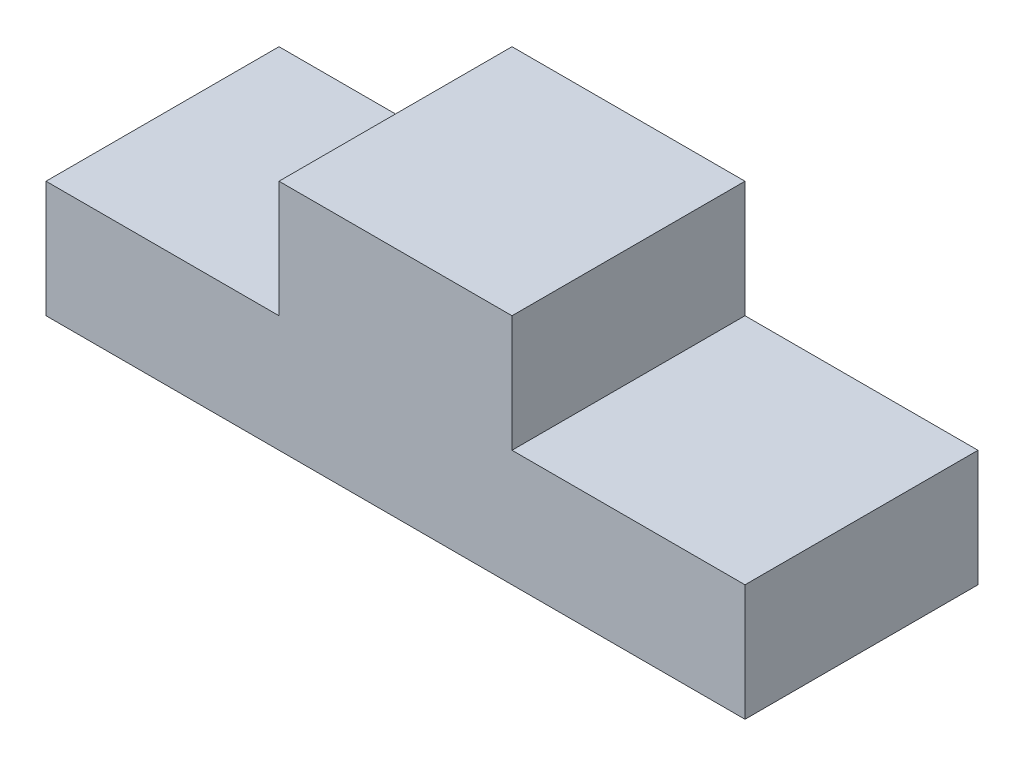
SolidWorks part; units mm, degrees
ref_plane "Front Plane" through (0, 0, 0) normal (0, 0, 1) x (1, 0, 0)
ref_plane "Top Plane" through (0, 0, 0) normal (0, 1, 0) x (1, 0, 0)
ref_plane "Right Plane" through (0, 0, 0) normal (1, 0, 0) x (0, 0, -1)
sketch "Sketch1" plane through (0, 0, 0) normal (0, 0, 1) x (1, 0, 0)
  line L0 (0, 12.7) -> (25.4, 12.7)
  line L1 (0, 0) -> (76.2, 0)
  line L2 (0, 0) -> (0, 12.7)
  line L3 (25.4, 25.4) -> (50.8, 25.4)
  line L4 (76.2, 0) -> (76.2, 12.7)
  line L5 (25.4, 12.7) -> (25.4, 25.4)
  line L6 (50.8, 25.4) -> (50.8, 12.7)
  line L7 (50.8, 12.7) -> (76.2, 12.7)
  dimension "D1" = 12.7
  dimension "D2" = 76.2
  dimension "D3" = 25.4
  dimension "D4" = 25.4
  dimension "D5" = 25.4
  dimension "D6" = 12.7
extrude "Boss-Extrude1" add sketch "Sketch1" against normal blind 25.4
